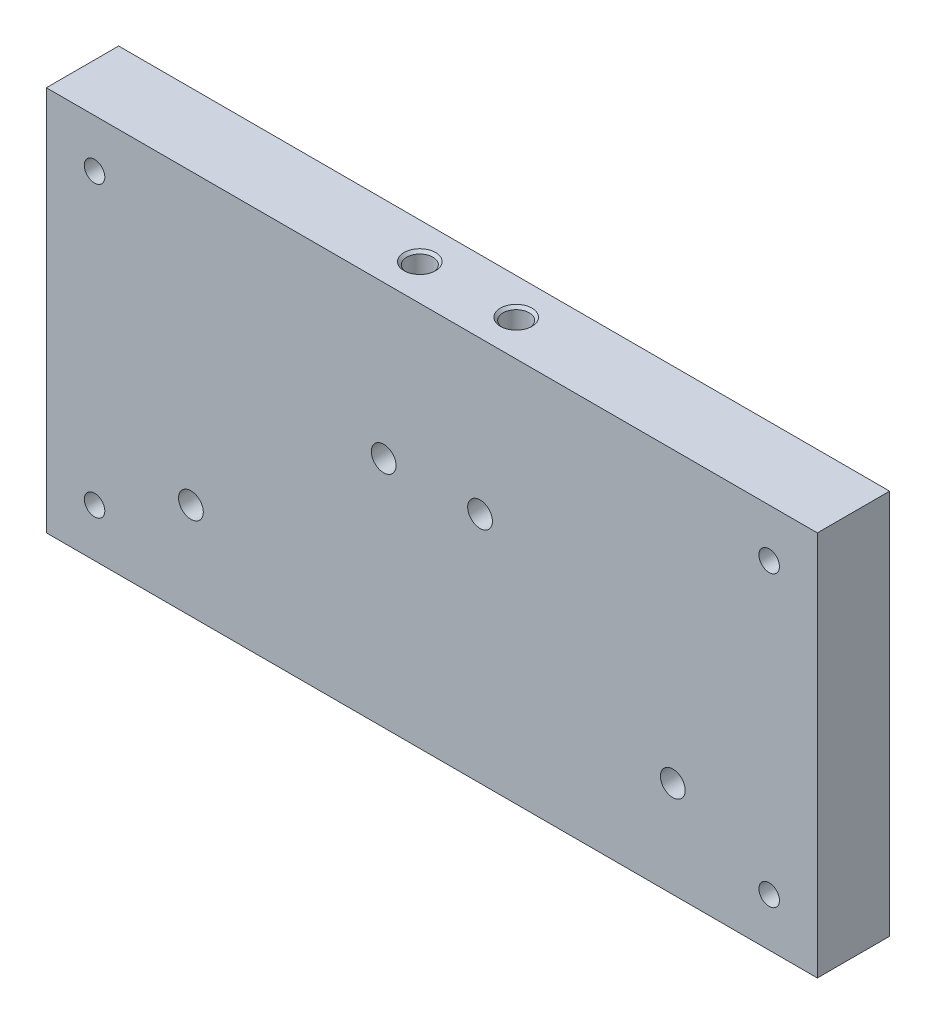
SolidWorks part; units mm, degrees
material "6061-T6 (SS)"
ref_plane "Front Plane" through (0, 0, 0) normal (0, 0, 1) x (1, 0, 0)
ref_plane "Top Plane" through (0, 0, 0) normal (0, 1, 0) x (1, 0, 0)
ref_plane "Right Plane" through (0, 0, 0) normal (1, 0, 0) x (0, 0, -1)
sketch "Sketch1" plane through (0, 0, 0) normal (0, 0, 1) x (1, 0, 0)
  line L1 (0, 0) -> (-101.6, 0)
  line L2 (0, 0) -> (0, 50.8)
  line L3 (0, 50.8) -> (-101.6, 50.8)
  line L4 (-101.6, 0) -> (-101.6, 50.8)
  dimension "D1" = 101.6
  dimension "D2" = 50.8
extrude "Boss-Extrude1" add sketch "Sketch1" along normal blind 9.525
sketch "Sketch5" plane through (0, 50.8, 0) normal (0, 1, 0) x (1, 0, 0)
  line L0 (-101.6, -4.7625) -> (0, -4.7625) construction
  line L1 (-101.6, -9.525) -> (-101.6, 0) construction
  line L2 (0, -9.525) -> (0, 0) construction
  line L3 (-57.15, -4.7625) -> (-44.45, -4.7625)
  point P8 (-50.8, -4.7625)
  dimension "D1" = 12.7
hole_wizard "#8-32 Tapped Hole1" positions "Sketch6" profile "Sketch8" tap size "#8-32" standard "ANSI Inch"
sketch "Sketch6" plane through (0, 50.8, 0) normal (0, 1, 0) x (1, 0, 0)
  point P0 (-44.45, -4.7625)
  point P3 (-57.15, -4.7625)
sketch "Sketch8" plane through (-44.45, 50.8, 4.7625) normal (1, 0, 0) x (0, 0, 1)
  line L0 (0, 0) -> (0, 20.0878)
  line L1 (0, 20.0878) -> (1.7272, 19.05)
  line L2 (1.7272, 19.05) -> (1.7272, 0.3556)
  line L3 (1.7272, 0.3556) -> (2.0828, 0)
  line L5 (2.0828, 0) -> (0, 0)
  line L6 (-1.7272, 0.3556) -> (-2.0828, 0) construction
  line L10 (0, 20.0878) -> (-1.7272, 19.05) construction
  line L11 (0, -6.35) -> (0, 107.95) construction
  dimension "Tap Drill Dia." = 3.4544
  dimension "Tap Drill Depth" = 19.05
  dimension "Near C'Sink Dia." = 4.1656
  dimension "Near C'Sink Angle" = 90
  dimension "Drill Angle" = 118
cosmetic thread "Hole Thread1" parameters "D1"=12.7, "D2"=4.1656
cosmetic thread "Hole Thread2" parameters "D1"=12.7, "D2"=4.1656
hole_wizard "#4 Clearance Hole2" positions "Sketch11" profile "Sketch12" hole size "#4" standard "ANSI Inch"
sketch "Sketch11" plane through (0, 0, 9.525) normal (0, 0, 1) x (1, 0, 0)
  line L0 (-44.45, 30.7122) -> (-42.7228, 31.75) construction
  line L1 (-57.15, 30.7122) -> (-55.4228, 31.75) construction
  line L2 (-44.45, 30.7122) -> (-42.7228, 31.75)
  line L3 (-57.15, 30.7122) -> (-55.4228, 31.75)
  point P1 (-44.45, 30.7122)
  point P3 (-57.15, 30.7122)
sketch "Sketch12" plane through (-44.45, 30.7122, 9.525) normal (1, 0, 0) x (0, -1, 0)
  line L0 (0, 0) -> (0, 26.3806)
  line L1 (0, 26.3806) -> (1.6319, 25.4)
  line L2 (1.6319, 25.4) -> (1.6319, 0)
  line L5 (1.6319, 0) -> (0, 0)
  line L10 (0, 26.3806) -> (-1.632, 25.4) construction
  line L11 (0, -6.35) -> (0, 107.95) construction
  dimension "Hole Dia." = 3.2639
  dimension "Hole Depth" = 25.4
  dimension "Drill Angle" = 118
sketch "Sketch13" plane through (0, 0, 9.525) normal (0, 0, 1) x (1, 0, 0)
  line L8 (-6.35, 6.35) -> (-6.35, 44.45)
  line L9 (-6.35, 44.45) -> (-95.25, 44.45)
  line L10 (-95.25, 44.45) -> (-95.25, 6.35)
  line L11 (-95.25, 6.35) -> (-6.35, 6.35)
  line L12 (-6.35, 6.35) -> (-6.35, 44.45)
  line L13 (-6.35, 44.45) -> (-95.25, 44.45)
  line L14 (-95.25, 44.45) -> (-95.25, 6.35)
  line L15 (-95.25, 6.35) -> (-6.35, 6.35)
  dimension "D1" = 6.35
hole_wizard "#6-32 Tapped Hole1" positions "Sketch14" profile "Sketch16" tap size "#6-32" standard "ANSI Inch" end condition through all
sketch "Sketch14" plane through (0, 0, 9.525) normal (0, 0, 1) x (1, 0, 0)
  point P0 (-95.25, 6.35)
  point P3 (-95.25, 44.45)
  point P6 (-6.35, 6.35)
  point P9 (-6.35, 44.45)
sketch "Sketch16" plane through (-95.25, 6.35, 9.525) normal (1, 0, 0) x (0, -1, 0)
  line L0 (0, 0) -> (0, 9.525)
  line L1 (0, 9.525) -> (1.3525, 9.525)
  line L2 (1.3525, 9.525) -> (1.3525, 0)
  line L5 (1.3525, 0) -> (0, 0)
  line L11 (0, -6.35) -> (0, 107.95) construction
  dimension "Thru Tap Drill Dia." = 2.7051
  dimension "Thru Tap Drill Depth" = 9.525
cosmetic thread "Hole Thread3" parameters "D2"=3.5052
cosmetic thread "Hole Thread4" parameters "D2"=3.5052
cosmetic thread "Hole Thread5" parameters "D2"=3.5052
cosmetic thread "Hole Thread6" parameters "D2"=3.5052
sketch "Sketch17" plane through (0, 0, 9.525) normal (0, 0, 1) x (1, 0, 0)
  line L0 (-82.55, 12.7) -> (-19.05, 12.7)
  line L1 (-82.55, 12.7) -> (-101.6, 12.7)
  line L2 (-101.6, 50.8) -> (-101.6, 0) construction
  line L3 (-19.05, 12.7) -> (0, 12.7)
  line L4 (0, 0) -> (0, 50.8) construction
  line L5 (-101.6, 0) -> (0, 0) construction
  dimension "D1" = 63.5
  dimension "D2" = 12.7
hole_wizard "#4 Clearance Hole1" positions "Sketch18" profile "Sketch20" hole size "#4" standard "ANSI Inch" end condition up to next
sketch "Sketch18" plane through (0, 0, 9.525) normal (0, 0, 1) x (1, 0, 0)
  point P0 (-82.55, 12.7)
  point P3 (-19.05, 12.7)
sketch "Sketch20" plane through (-82.55, 12.7, 9.525) normal (1, 0, 0) x (0, -1, 0)
  line L0 (0, 0) -> (0, 9.525)
  line L1 (0, 9.525) -> (1.6319, 9.525)
  line L2 (1.6319, 9.525) -> (1.6319, 0)
  line L5 (1.6319, 0) -> (0, 0)
  line L11 (0, -6.35) -> (0, 107.95) construction
  dimension "Thru Hole Dia." = 3.2639
  dimension "Thru Hole Depth" = 9.525
